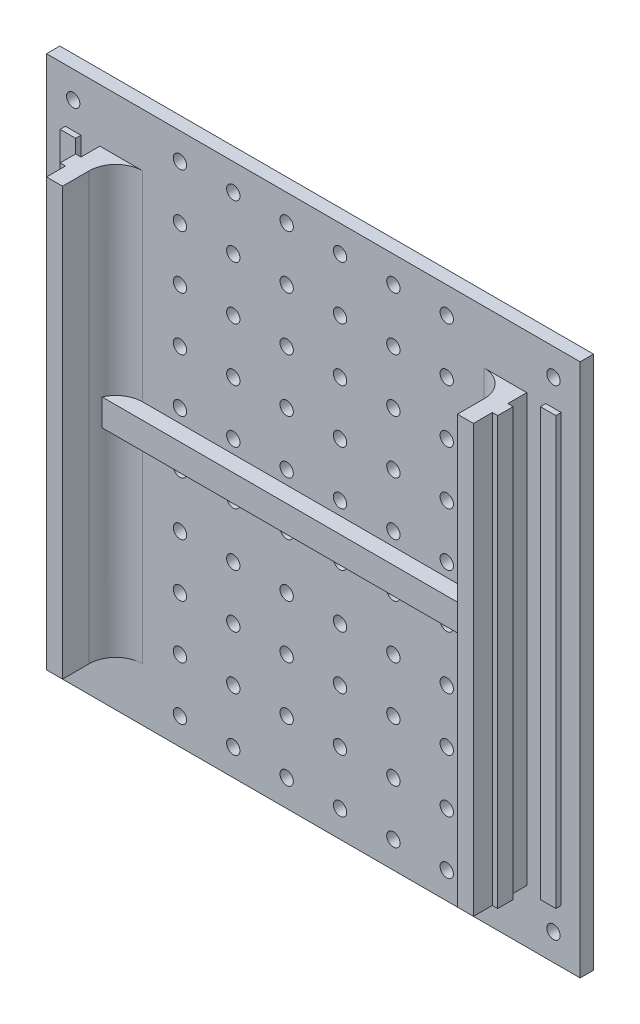
SolidWorks part; units mm, degrees
ref_plane "Front Plane" through (0, 0, 0) normal (0, 0, 1) x (1, 0, 0)
ref_plane "Top Plane" through (0, 0, 0) normal (0, 1, 0) x (1, 0, 0)
ref_plane "Right Plane" through (0, 0, 0) normal (1, 0, 0) x (0, 0, -1)
sketch "Sketch1" plane through (0, 0, 0) normal (0, 0, 1) x (1, 0, 0)
  line L1 (-50, -50) -> (50, -50)
  line L2 (-50, -50) -> (-50, 50)
  line L3 (-50, 50) -> (50, 50)
  line L4 (50, -50) -> (50, 50)
  line L5 (-50, -50) -> (50, 50) construction
  line L6 (-50, 50) -> (50, -50) construction
  point P0 (0, 0)
  dimension "D1" = 100
  dimension "D2" = 100
extrude "Main" add sketch "Sketch1" along normal blind 12.5
sketch "Sketch2" plane through (0, 0, 0) normal (0, 1, 0) x (1, 0, 0)
  line L0 (-40, -8.95) -> (-40, -12.5)
  line L1 (50, -12.5) -> (-50, -12.5) construction
  line L2 (-50, -2.5) -> (-46.45, -2.5)
  line L3 (-46.45, -2.5) -> (-46.45, -3.5)
  line L4 (-46.45, -3.5) -> (-43.55, -3.5)
  line L5 (-43.55, -3.5) -> (-43.55, -2.5)
  line L6 (-43.55, -2.5) -> (-40, -2.5)
  line L9 (-40, -2.5) -> (-40, -6.05)
  line L10 (-40, -6.05) -> (-41, -6.05)
  line L11 (-41, -6.05) -> (-41, -8.95)
  line L12 (-41, -8.95) -> (-40, -8.95)
  line L15 (-50, -12.5) -> (-50, 0) construction
  line L16 (-50, -2.5) -> (-50, -12.5)
  line L17 (-50, -12.5) -> (-40, -12.5)
  dimension "D1" = 10
  dimension "D2" = 10
  dimension "D3" = 1
  dimension "D4" = 2.9
extrude "Cut-Extrude1" cut sketch "Sketch2" against normal through all and the other way through all
mirror "Mirror1" about plane through (0, 0, 0) normal (1, 0, 0) of "Cut-Extrude1"
sketch "Sketch3" plane through (0, 50, 0) normal (0, 1, 0) x (1, 0, 0)
  line L0 (40, -12.5) -> (-40, -12.5) construction
  line L1 (-37, -12.5) -> (37, -12.5)
  line L2 (-37, -12.5) -> (-37, -2.5)
  line L3 (-37, -2.5) -> (37, -2.5)
  line L4 (37, -12.5) -> (37, -2.5)
  line L5 (-40, -2.5) -> (-40, -6.05) construction
  line L6 (40, -2.5) -> (40, -6.05) construction
  line L10 (-50, 0) -> (50, 0) construction
  point P10 (40, -4.275)
  dimension "D1" = 3
  dimension "D2" = 3
  dimension "D3" = 2.5
extrude "Cut-Extrude2" cut sketch "Sketch3" against normal through all
fillet "Fillet1" radius 5 2 edges at (-37, 0, 2.5) (37, 0, 2.5)
sketch "Sketch9" plane through (0, 0, 2.5) normal (0, 0, 1) x (1, 0, 0)
  line L1 (-40, 2.5) -> (40, 2.5)
  line L2 (-40, 2.5) -> (-40, -2.5)
  line L3 (-40, -2.5) -> (40, -2.5)
  line L4 (40, 2.5) -> (40, -2.5)
  line L5 (40, -50) -> (40, 50) construction
  line L6 (-40, -50) -> (-40, 50) construction
  line L7 (6.875, 0) -> (-6.875, 0) construction
  point P4 (-40, 2.5)
  point P6 (41, -3.6007)
  point P7 (39.5548, -2.5)
  point P8 (35, 0)
  point P9 (40, 0)
  point P11 (35, 0.8619)
  point P12 (0, 0)
  point P13 (35, 0.8891)
  point P15 (41, -1.1007)
  point P16 (41, 0)
  dimension "D1" = 5
extrude "Boss-Extrude1" add sketch "Sketch9" along normal blind 3
sketch "Sketch4" plane through (0, 0, 2.5) normal (0, 0, 1) x (1, 0, 0)
  circle A0 centre (25, -45) radius 1.25
  dimension "D1" = 2.5
  dimension "D2" = 45
  dimension "D3" = 25
extrude "FixHole" cut sketch "Sketch4" against normal through all
pattern_linear "LPattern1" count 6 spacing 10 along (-1, 0, 0) count 10 spacing 10 along (0, 1, 0) of "FixHole"
sketch "Sketch6" plane through (0, 0, 2.5) normal (0, 0, 1) x (1, 0, 0)
  circle A0 centre (0, 0) radius 1.25
  dimension "D1" = 2.5
extrude "CentralHole" cut sketch "Sketch6" against normal through all
sketch "Sketch7" plane through (0, 0, 12.5) normal (0, 0, -1) x (-1, 0, 0)
  line L0 (-50, -50) -> (-50, 50) construction
  line L1 (50, -50) -> (-50, -50)
  line L2 (50, -50) -> (50, -40)
  line L3 (50, -40) -> (-50, -40)
  line L4 (-50, -50) -> (-50, -40)
  line L6 (50, 50) -> (-50, 50)
  line L7 (50, 50) -> (50, 40)
  line L8 (50, 40) -> (-50, 40)
  line L9 (-50, 50) -> (-50, 40)
  dimension "D1" = 10
extrude "Cut-Extrude3" cut sketch "Sketch7" along normal up to surface (10 mm away) up to face at (48.225, 0, 2.5)
sketch "Sketch8" plane through (0, 0, 2.5) normal (0, 0, 1) x (1, 0, 0)
  line L0 (0, -6.875) -> (0, 6.875) construction
  line L1 (6.875, 0) -> (-6.875, 0) construction
  circle A0 centre (-45, 45) radius 1.25
  dimension "D1" = 2.5
  dimension "D2" = 45
  dimension "D3" = 45
extrude "Cut-Extrude4" cut sketch "Sketch8" against normal through all
pattern_linear "LPattern2" count 2 spacing 90 along (1, 0, 0) count 2 spacing 90 along (0, -1, 0) of "Cut-Extrude4"
